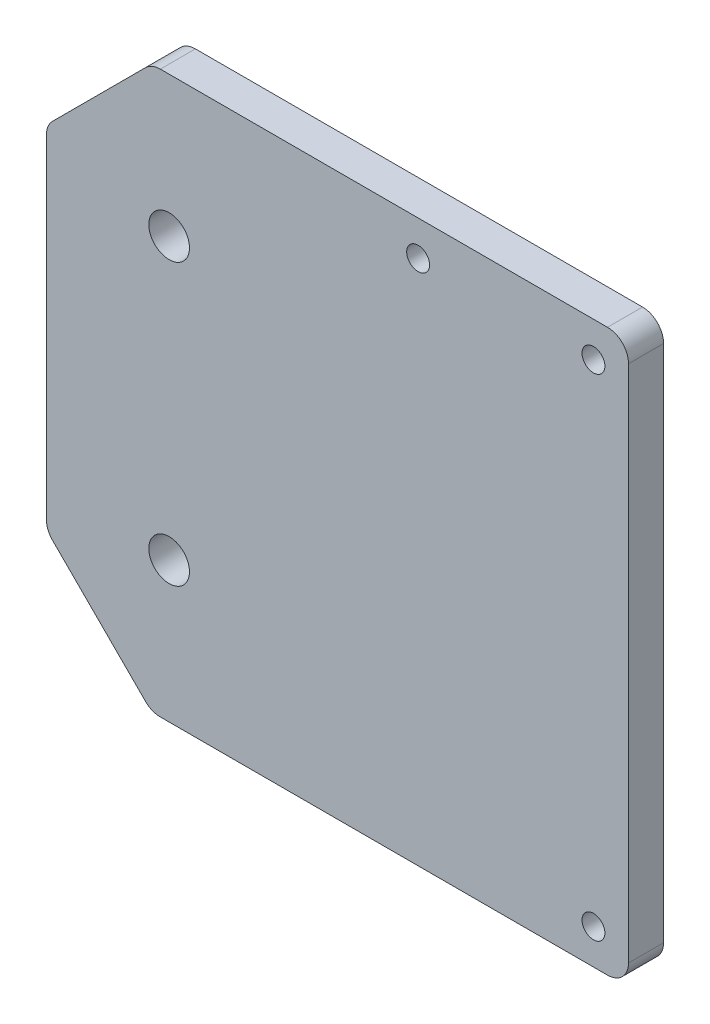
SolidWorks part; units mm, degrees
ref_plane "Front Plane" through (0, 0, 0) normal (0, 0, 1) x (1, 0, 0)
ref_plane "Top Plane" through (0, 0, 0) normal (0, 1, 0) x (1, 0, 0)
ref_plane "Right Plane" through (0, 0, 0) normal (1, 0, 0) x (0, 0, -1)
sketch "Base" plane through (0, 0, 0) normal (0, 0, 1) x (1, 0, 0)
  line L1 (-39.7758, 40) -> (-39.7758, -40)
  line L4 (-17.7758, -40) -> (43.2242, -40)
  line L8 (-22.2758, 20) -> (-22.2758, -20) construction
  line L9 (12.7242, -0.745) -> (12.7242, -28.495) construction
  line L10 (19.7242, -2.87) -> (5.7242, -2.87)
  line L11 (19.7242, -2.87) -> (19.7242, -26.37)
  line L12 (19.7242, -26.37) -> (5.7242, -26.37)
  line L13 (5.7242, -2.87) -> (5.7242, -26.37)
  line L14 (33.2242, 30) -> (33.2242, -30) construction
  line L15 (33.2242, 1) -> (43.2242, 1) construction
  line L16 (43.2242, 40) -> (43.2242, -40)
  line L18 (-17.7758, -40) -> (-39.7758, -40)
  line L19 (33.2242, -30) -> (33.2242, -40) construction
  line L20 (33.2242, 30) -> (43.2242, 40) construction
  line L21 (-39.7758, 40) -> (43.2242, 40)
  line L24 (33.2242, 30) -> (5.7242, 30) construction
  line L25 (5.7242, 30) -> (5.7242, 40) construction
  line L26 (5.7242, -40) -> (5.7242, -30) construction
  line L27 (5.7242, -30) -> (33.2242, -30) construction
  circle A0 centre (12.7242, -20) radius 17.5 construction
  point P2 (30.2242, -20)
  point P7 (24.1741, 0)
  point P9 (12.7242, -40)
  point P10 (-39.7758, 0)
  point P11 (-22.2758, -20)
  point P12 (-22.2758, 20)
  point P15 (-22.2758, 0)
  point P20 (12.7242, -2.87)
  point P22 (19.7242, -14.62)
  point P23 (12.7242, 20)
  point P24 (-22.2758, -20)
  point P25 (-22.2758, 20)
  point P26 (12.7242, -0.745)
  point P27 (12.7242, -28.495)
  point P30 (12.7242, -14.62)
  point P31 (12.7242, -20)
  point P33 (12.7242, -2.5)
  point P41 (38.2242, -35)
  point P43 (38.2242, 35)
  point P44 (13.2242, 35)
  point P45 (5.7242, 35)
  point P46 (38.2242, 1)
  point P47 (33.2242, -35)
  dimension "D11" = 35
  dimension "D2" = 23.5
  dimension "D1" = 14
  dimension "D4" = 35
  dimension "D9" = 27.75
  dimension "D3" = 40
  dimension "D10" = 6.37
  dimension "D5" = 17.5
  dimension "D14" = 10
  dimension "D7" = 80
  dimension "D8" = 10
  dimension "D12" = 3.5
  dimension "D6" = 3
  dimension "D13" = 7.5
sketch "Hole_sketch" plane through (0, 0, 0) normal (0, 0, 1) x (1, 0, 0)
  point P0 (-22.2758, -20)
  point P2 (-22.2758, 20)
  point P4 (12.7242, -0.745)
  point P6 (12.7242, -28.495)
extrude "Main" add sketch "Base" along normal blind 5
hole_wizard "Gear Axis Holes" positions "Sketch9" profile "Sketch8" hole size "Ø5.8" standard "ANSI Metric" end condition through all
sketch "Sketch9" plane through (0, 0, 5) normal (0, 0, -1) x (-1, 0, 0)
  point P0 (22.2758, -20)
  point P3 (22.2758, 20)
sketch "Sketch8" plane through (-22.2758, -20, 5) normal (1, 0, 0) x (0, -1, 0)
  line L0 (0, 0) -> (0, 5)
  line L1 (0, 5) -> (2.9, 5)
  line L2 (2.9, 5) -> (2.9, 0)
  line L5 (2.9, 0) -> (0, 0)
  line L11 (0, -6.35) -> (0, 107.95) construction
  dimension "Thru Hole Dia." = 5.8
  dimension "Thru Hole Depth" = 5
sketch "Sketch13" plane through (0, 0, 5) normal (0, 0, 1) x (1, 0, 0)
  line L10 (33.2242, 30) -> (33.2242, -30) construction
  line L11 (33.2242, 30) -> (5.7242, 30) construction
  line L12 (5.7242, 30) -> (5.7242, 40) construction
  line L13 (-39.7758, 40) -> (43.2242, 40) construction
  line L15 (43.2242, 40) -> (43.2242, -40) construction
  line L17 (33.2242, 30) -> (33.2242, 1)
  line L18 (33.2242, 30) -> (5.7242, 30)
  line L19 (5.7242, 30) -> (5.7242, 40)
  line L20 (5.7242, 40) -> (43.2242, 40)
  line L21 (43.2242, 40) -> (43.2242, 1)
  line L22 (33.2242, -30) -> (33.2242, -40) construction
  line L23 (-17.7758, -40) -> (43.2242, -40) construction
  line L24 (33.2242, -30) -> (33.2242, -40)
  line L25 (33.2242, 30) -> (33.2242, -30)
  line L26 (33.2242, -40) -> (43.2242, -40)
  line L27 (43.2242, 40) -> (43.2242, -40)
chamfer "Chamfer1" distance 15 angle 45 2 edges at (-39.7758, -40, 2.5) (-39.7758, 40, 2.5)
fillet "Fillet6" radius 3 6 edges at (-24.7758, -40, 2.5) (-39.7758, -25, 2.5) (-39.7758, 25, 2.5) (-24.7758, 40, 2.5) (43.2242, 40, 2.5) (43.2242, -40, 2.5)
hole_wizard "#4 Clearance Hole1" positions "Sketch15" profile "Sketch14" hole size "#4" standard "ANSI Inch" end condition through all
sketch "Sketch15" plane through (0, 0, 5) normal (0, 0, 1) x (1, 0, 0)
  point P1 (13.2242, 35)
  point P3 (38.2242, 35)
  point P5 (38.2242, -35)
sketch "Sketch14" plane through (13.2242, 35, 5) normal (1, 0, 0) x (0, -1, 0)
  line L0 (0, 0) -> (0, 5)
  line L1 (0, 5) -> (1.6319, 5)
  line L2 (1.6319, 5) -> (1.6319, 0)
  line L5 (1.6319, 0) -> (0, 0)
  line L11 (0, -6.35) -> (0, 107.95) construction
  dimension "Thru Hole Dia." = 3.2639
  dimension "Thru Hole Depth" = 5
equation "\"D_gear-axes\"= 40mm"
equation "\"D_gear-servo\"= 35mm"
equation "\"W_servo\"= 23mm"
equation "\"W_servo-center\"= 6.37mm"
equation "\"D1@Base\"=\"L_servo\"+1"
equation "\"D2@Base\"=\"W_servo\"+0.5"
equation "\"L_servo\"= 13mm"
equation "\"D4@Base\" = \"D_gear-servo\""
equation "\"D9@Base\"=27.75"
equation "\"D_servo-holes\"= 3.1mm"
equation "\"D3@Base\"=\"D_gear-axes\""
equation "\"D10@Base\"=\"W_servo-center\""
